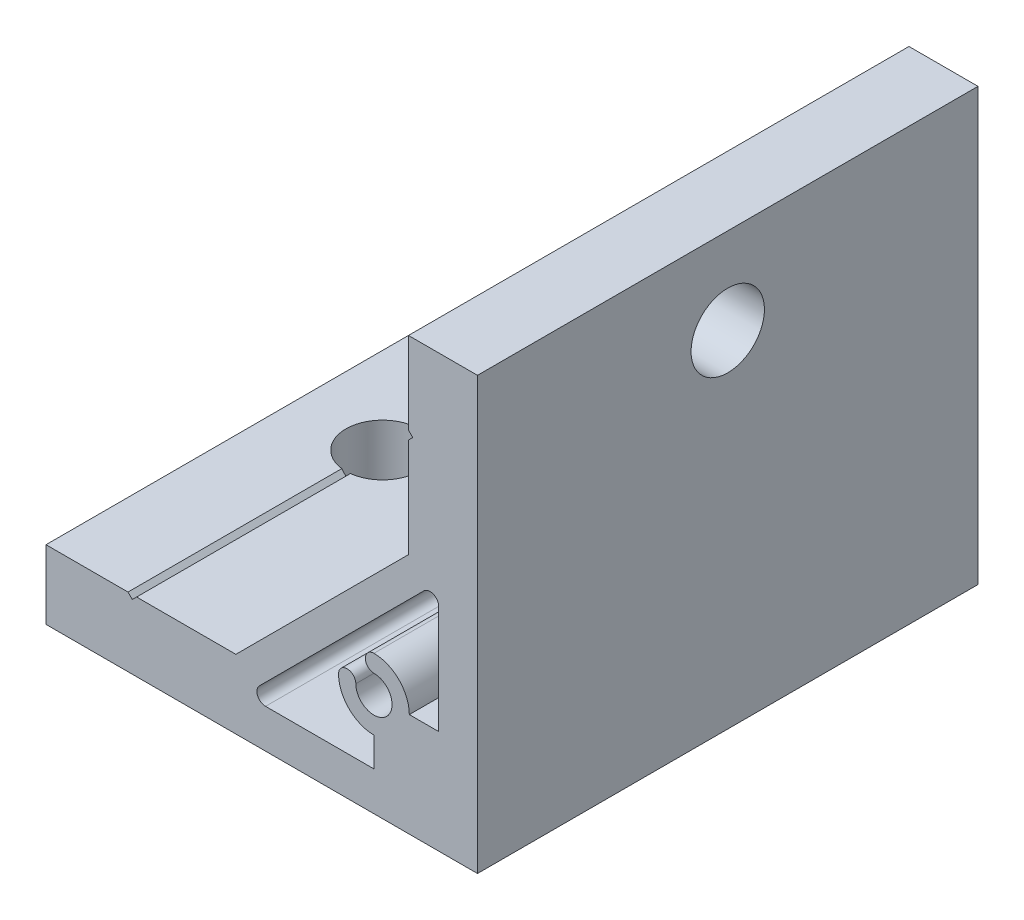
SolidWorks part; units mm, degrees
material "6063 T5"
ref_plane "Спереди" through (0, 0, 0) normal (0, 0, 1) x (1, 0, 0)
ref_plane "Сверху" through (0, 0, 0) normal (0, 1, 0) x (1, 0, 0)
ref_plane "Справа" through (0, 0, 0) normal (1, 0, 0) x (0, 0, -1)
sketch "Эскиз1" plane through (0, 0, 0) normal (0, 0, 1) x (1, 0, 0)
  line L0 (-50, 0) -> (0, 0)
  line L1 (0, 0) -> (0, 50)
  line L2 (0, 50) -> (-8, 50)
  line L3 (-8, 50) -> (-8, 40.5)
  line L4 (-8, 40.5) -> (-7.5, 40)
  line L5 (-7.5, 40) -> (-8, 39.5)
  line L6 (-8, 39.5) -> (-8, 28)
  line L7 (-8, 28) -> (-28, 8)
  line L8 (-28, 8) -> (-39.5, 8)
  line L9 (-39.5, 8) -> (-40, 7.5)
  line L10 (-40, 7.5) -> (-40.5, 8)
  line L11 (-40.5, 8) -> (-50, 8)
  line L12 (-50, 8) -> (-50, 0)
  line L13 (-4.5, 12) -> (-4.5, 24.5603)
  line L14 (-6.2071, 25.2674) -> (-25.2674, 6.2071)
  line L15 (-24.5603, 4.5) -> (-12, 4.5)
  line L16 (-12, 4.5) -> (-12, 7.9)
  line L17 (-7.9, 12) -> (-4.5, 12)
  arc A0 (-4.5, 24.5603) -> (-6.2071, 25.2674) centre (-5.5, 24.5603) ccw
  arc A1 (-25.2674, 6.2071) -> (-24.5603, 4.5) centre (-24.5603, 5.5) ccw
  arc A2 (-12, 7.9) -> (-16.1, 12) centre (-12, 12) cw
  arc A3 (-16.1, 12) -> (-14.1, 12) centre (-15.1, 12) cw
  arc A4 (-14.1, 12) -> (-12, 14.1) centre (-12, 12) ccw
  arc A5 (-12, 14.1) -> (-12, 16.1) centre (-12, 15.1) cw
  arc A6 (-12, 16.1) -> (-7.9, 12) centre (-12, 12) cw
  dimension "D6" = 4.2
  dimension "D7" = 1
  dimension "D9" = 1
  dimension "D1" = 50
  dimension "D2" = 8
  dimension "D3" = 135
  dimension "D4" = 12
  dimension "D5" = 12
  dimension "D8" = 28
  dimension "D10" = 3.2
  dimension "D11" = 4.5
  dimension "D12" = 40
  dimension "D13" = 1
extrude "Бобышка-Вытянуть1" add sketch "Эскиз1" along normal mid plane 58
sketch "Эскиз2" plane through (-8, 0, 0) normal (-1, 0, 0) x (0, 0, 1)
  line L0 (29, 40) -> (-29, 40) construction
  circle A0 centre (0, 40) radius 4.25
  dimension "D1" = 8.5
extrude "Вырез-Вытянуть1" cut sketch "Эскиз2" against normal through all
sketch "Эскиз3" plane through (0, 8, 0) normal (0, 1, 0) x (1, 0, 0)
  line L0 (-40, -29) -> (-40, 29) construction
  circle A0 centre (-40, 0) radius 4.25
  dimension "D1" = 8.5
extrude "Вырез-Вытянуть2" cut sketch "Эскиз3" against normal through all
